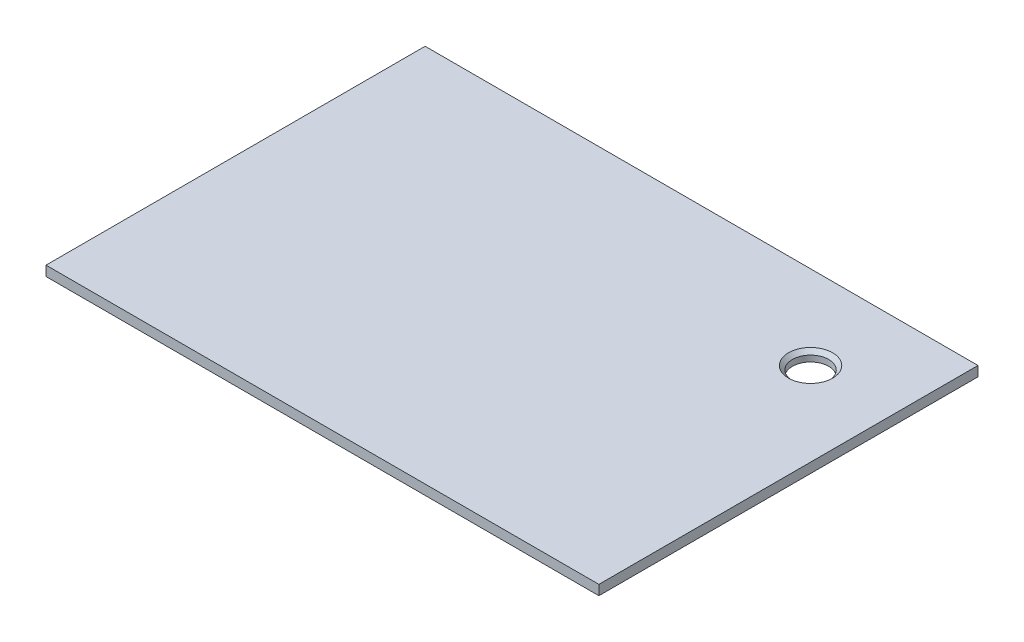
SolidWorks part; units mm, degrees
ref_plane "Front Plane" through (0, 0, 0) normal (0, 0, 1) x (1, 0, 0)
ref_plane "Top Plane" through (0, 0, 0) normal (0, 1, 0) x (1, 0, 0)
ref_plane "Right Plane" through (0, 0, 0) normal (1, 0, 0) x (0, 0, -1)
sketch "Sketch1" plane through (0, 0, 0) normal (0, 1, 0) x (1, 0, 0)
  line L1 (0, 0) -> (175, 0)
  line L2 (0, 0) -> (0, 120)
  line L3 (0, 120) -> (175, 120)
  line L4 (175, 0) -> (175, 120)
extrude "Boss-Extrude1" add sketch "Sketch1" along normal blind 3.125
hole_wizard "1/2-20 Tapped Hole1" positions "Sketch5" profile "Sketch3" tap size "1/2-20" standard "ANSI Inch"
sketch "Sketch5" plane through (0, 3.125, 0) normal (0, 1, 0) x (1, 0, 0)
  line L0 (175, 0) -> (175, 120) construction
  line L1 (175, 120) -> (0, 120) construction
  point P0 (148.5, 93.5)
  dimension "D1" = 26.5
  dimension "D2" = 26.5
sketch "Sketch3" plane through (148.5, 3.125, -93.5) normal (1, 0, 0) x (0, 0, 1)
  line L0 (0, 0) -> (0, 33.4576)
  line L1 (0, 33.4576) -> (5.7544, 30)
  line L2 (5.7544, 30) -> (5.7544, 1.2306)
  line L3 (5.7544, 1.2306) -> (6.985, 0)
  line L5 (6.985, 0) -> (0, 0)
  line L6 (-5.7544, 1.2306) -> (-6.985, 0) construction
  line L10 (0, 33.4576) -> (-5.7544, 30) construction
  line L11 (0, -6.35) -> (0, 107.95) construction
  dimension "Tap Drill Dia." = 11.5087
  dimension "Tap Drill Depth" = 30
  dimension "Near C'Sink Dia." = 13.97
  dimension "Near C'Sink Angle" = 90
  dimension "Drill Angle" = 118
cosmetic thread "Hole Thread1"
